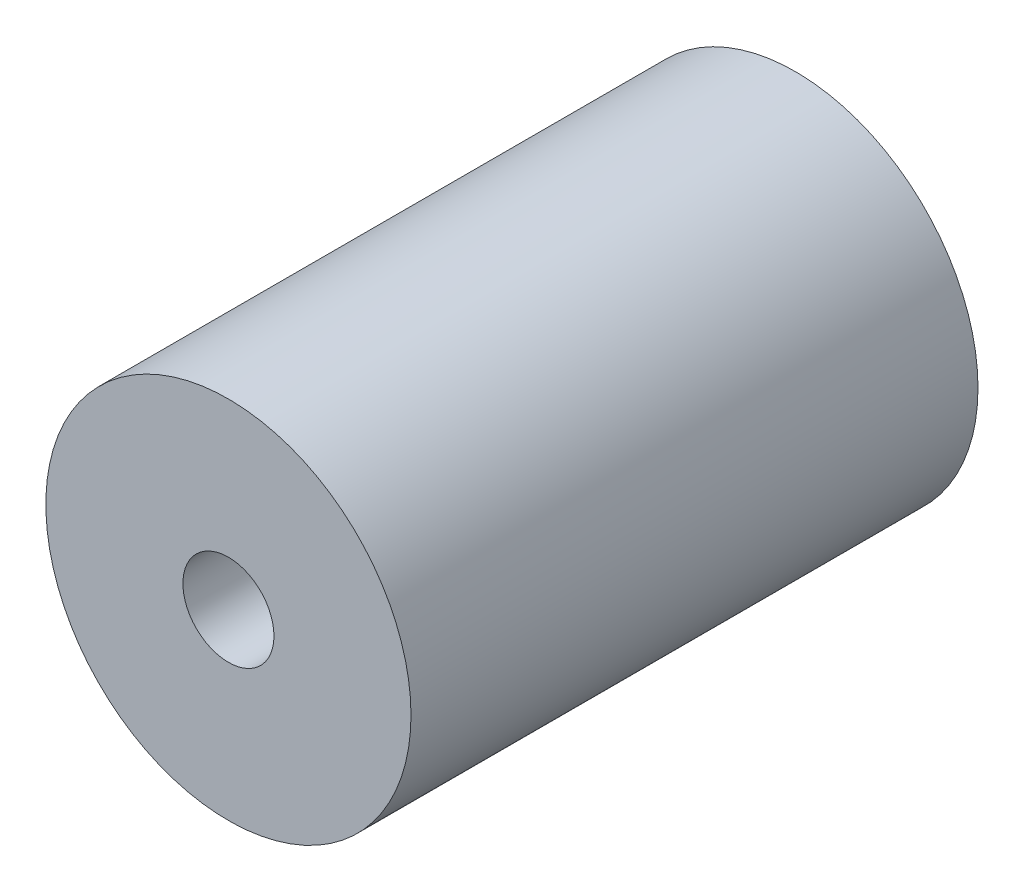
SolidWorks part; units mm, degrees
ref_plane "Front Plane" through (0, 0, 0) normal (0, 0, 1) x (1, 0, 0)
ref_plane "Top Plane" through (0, 0, 0) normal (0, 1, 0) x (1, 0, 0)
ref_plane "Right Plane" through (0, 0, 0) normal (1, 0, 0) x (0, 0, -1)
sketch "Sketch1" plane through (0, 0, 0) normal (0, 0, 1) x (1, 0, 0)
  circle A0 centre (0, 0) radius 6.1341
  dimension "D1" = 12.2682
extrude "Boss-Extrude1" add sketch "Sketch1" along normal blind 19.05
sketch "Sketch2" plane through (0, 0, 19.05) normal (0, 0, 1) x (1, 0, 0)
  circle A0 centre (0, 0) radius 1.53
  dimension "D1" = 3.06
extrude "Cut-Extrude1" cut sketch "Sketch2" against normal through all
hole_wizard "1/4-20 Tapped Hole1" positions "Sketch4" profile "Sketch5" tap size "1/4-20" standard "ANSI Inch"
sketch "Sketch4" plane through (0, 0, 0) normal (0, 0, -1) x (-1, 0, 0)
  point P0 (0, 0)
sketch "Sketch5" plane through (0, 0, 0) normal (1, 0, 0) x (0, 1, 0)
  line L0 (0, 0) -> (0, 11.0588)
  line L1 (0, 11.0588) -> (2.5527, 9.525)
  line L2 (2.5527, 9.525) -> (2.5527, 0)
  line L5 (2.5527, 0) -> (0, 0)
  line L10 (0, 11.0588) -> (-2.5527, 9.525) construction
  line L11 (0, -6.35) -> (0, 107.95) construction
  dimension "Tap Drill Dia." = 5.1054
  dimension "Tap Drill Depth" = 9.525
  dimension "Drill Angle" = 118
